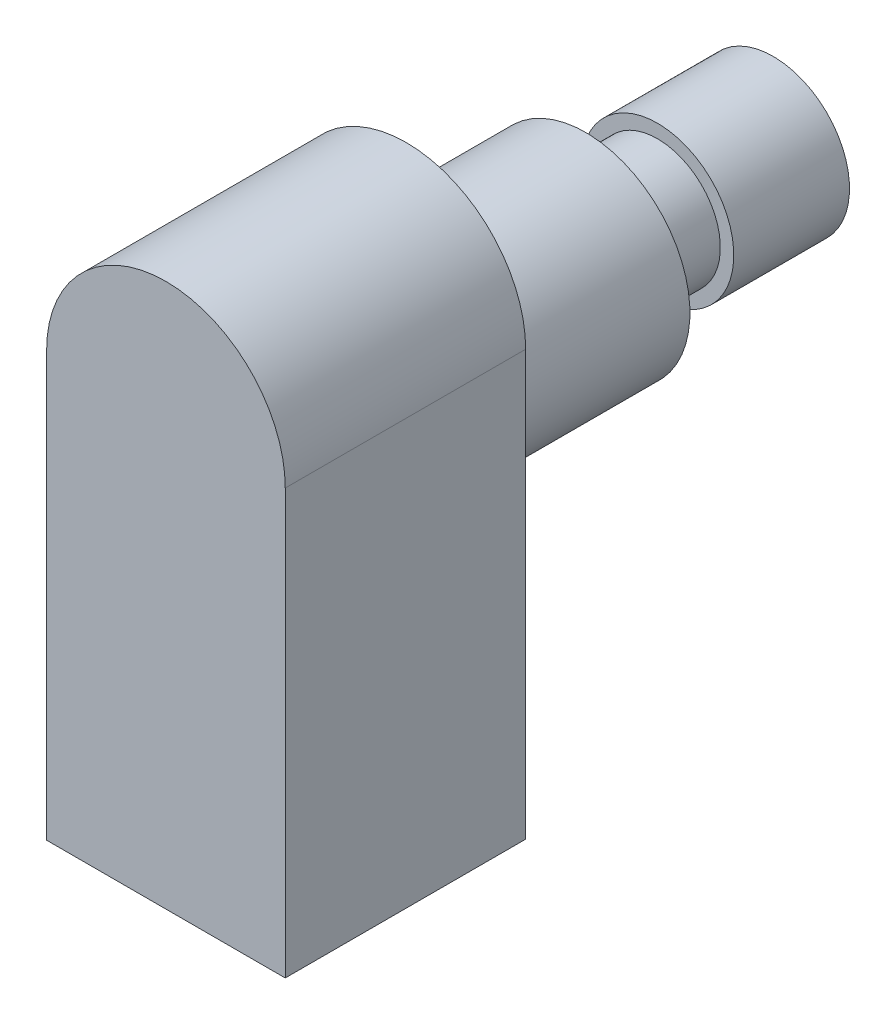
SolidWorks part; units mm, degrees
ref_plane "Plan de face" through (0, 0, 0) normal (0, 0, 1) x (1, 0, 0)
ref_plane "Plan de dessus" through (0, 0, 0) normal (0, 1, 0) x (1, 0, 0)
ref_plane "Plan de droite" through (0, 0, 0) normal (1, 0, 0) x (0, 0, -1)
sketch "Esquisse1" plane through (0, 0, 0) normal (0, 0, 1) x (1, 0, 0)
  line L0 (-6.65, 0) -> (-6.65, -23.65)
  line L1 (-6.65, -23.65) -> (6.65, -23.65)
  line L2 (6.65, -23.65) -> (6.65, 0)
  arc A0 (6.65, 0) -> (-6.65, 0) centre (0, 0) ccw
  dimension "D1" = 6.65
  dimension "D2" = 23.65
extrude "Boss.-Extru.1" add sketch "Esquisse1" along normal blind 13.4
sketch "Esquisse2" plane through (0, 0, 0) normal (0, 0, -1) x (-1, 0, 0)
  circle A0 centre (0, -3.665) radius 5.805
  point P2 (0, 0)
  dimension "D1" = 11.61
  dimension "D2" = 3.665
extrude "Boss.-Extru.2" add sketch "Esquisse2" along normal blind 10
sketch "Esquisse3" plane through (0, 0, -10) normal (0, 0, -1) x (-1, 0, 0)
  circle A0 centre (0, -3.665) radius 3.5
  dimension "D1" = 7
extrude "Boss.-Extru.3" add sketch "Esquisse3" along normal blind 4
sketch "Esquisse4" plane through (0, 0, -14) normal (0, 0, -1) x (-1, 0, 0)
  circle A0 centre (0, -3.665) radius 4.25
  circle A1 centre (0, -3.665) radius 3.5 construction
  dimension "D1" = 8.5
extrude "Boss.-Extru.4" add sketch "Esquisse4" along normal blind 6.45
